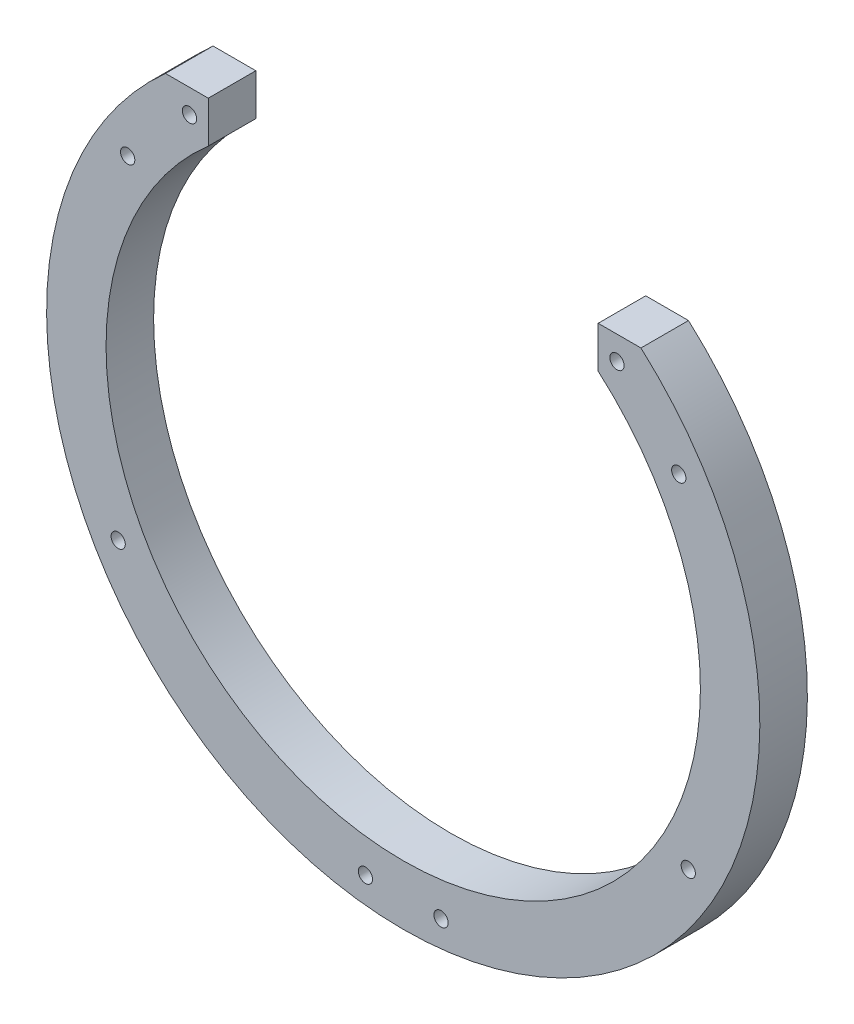
SolidWorks part; units mm, degrees
material "ABS"
ref_plane "Plano frontal" through (0, 0, 0) normal (0, 0, 1) x (1, 0, 0)
ref_plane "Plano superior" through (0, 0, 0) normal (0, 1, 0) x (1, 0, 0)
ref_plane "Plano direito" through (0, 0, 0) normal (1, 0, 0) x (0, 0, -1)
sketch "Esboço1" plane through (0, 0, 0) normal (0, 0, 1) x (1, 0, 0)
  line L0 (44.4954, -168.4305) -> (22.4463, -168.4305)
  line L1 (-33.4554, -168.4305) -> (-55.5046, -168.4305)
  line L10 (-55.5046, -168.4305) -> (-55.5734, -168.3931)
  arc A0 (-55.5046, -168.4305) -> (44.4954, -168.4305) centre (-5.5046, -224.3322) ccw
  arc A1 (-33.4554, -168.4305) -> (22.4463, -168.4305) centre (-5.5046, -224.3322) ccw
  dimension "D1" = 150
  dimension "D2" = 125
extrude "Ressalto-extrusão1" add sketch "Esboço1" along normal blind 10 contours A0 L0 A1 L1
sketch "Esboço2" plane through (0, 0, 10) normal (0, 0, 1) x (1, 0, 0)
  line L0 (44.4954, -168.4305) -> (22.4463, -168.4305) construction
  line L1 (-5.5046, -299.3322) -> (-5.5046, -271.3491) construction
  circle A0 centre (39.4463, -173.4305) radius 1.5
  circle A1 centre (52.4463, -187.4305) radius 1.5
  circle A2 centre (54.4463, -258.4305) radius 1.5
  circle A3 centre (-13.4554, -293.4305) radius 1.5
  circle A4 centre (2.4463, -293.4305) radius 1.5
  circle A5 centre (-65.4554, -258.4305) radius 1.5
  circle A8 centre (-63.4554, -187.4305) radius 1.5
  circle A9 centre (-50.4554, -173.4305) radius 1.5
  dimension "D1" = 5
  dimension "D2" = 17
  dimension "D3" = 3
  dimension "D4" = 30
  dimension "D5" = 19
  dimension "D6" = 3
  dimension "D7" = 20
  dimension "D8" = 125
  dimension "D9" = 3
  dimension "D10" = 90
  dimension "D11" = 32
  dimension "D12" = 3
extrude "Corte-extrusão1" cut sketch "Esboço2" against normal blind 10
sketch "Esboço3" plane through (0, 0, 10) normal (0, 0, 1) x (1, 0, 0)
  line L1 (35.4954, -180.8324) -> (-46.5046, -180.8324)
  line L2 (35.4954, -180.8324) -> (35.4954, -159.2566)
  line L3 (35.4954, -159.2566) -> (-46.5046, -159.2566)
  line L4 (-46.5046, -180.8324) -> (-46.5046, -159.2566)
  dimension "D1" = 9
  dimension "D2" = 9
extrude "Corte-extrusão2" cut sketch "Esboço3" against normal through all
